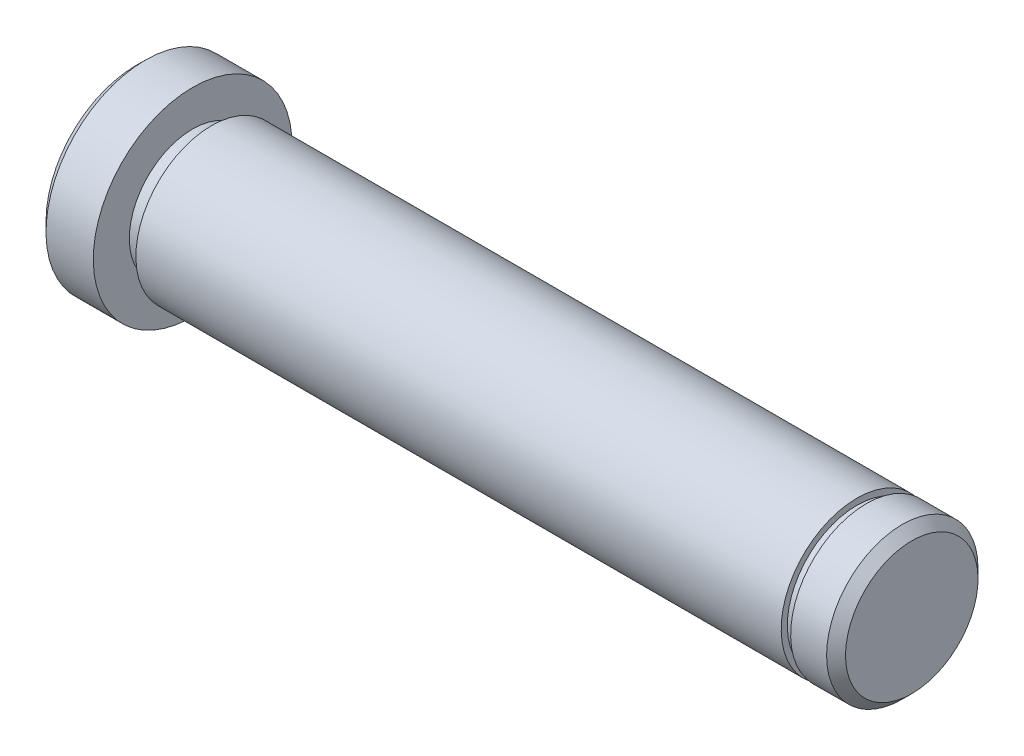
SolidWorks part; units mm, degrees
ref_plane "前视基准面" through (0, 0, 0) normal (0, 0, 1) x (1, 0, 0)
ref_plane "上视基准面" through (0, 0, 0) normal (0, 1, 0) x (1, 0, 0)
ref_plane "右视基准面" through (0, 0, 0) normal (1, 0, 0) x (0, 0, -1)
other "Configuration Table"
sketch "草图1" plane through (0, 0, 0) normal (0, 0, 1) x (1, 0, 0)
  line L0 (0, 0) -> (36.475, 0) construction
  line L1 (0, 0) -> (0, 10.5)
  line L2 (0, 10.5) -> (6, 10.5)
  line L3 (6, 10.5) -> (6, 8)
  line L4 (6, 8) -> (82, 8)
  line L5 (82, 8) -> (82, 0)
  line L6 (82, 0) -> (0, 0)
  line L7 (6, 8) -> (6, 6.6919)
  line L8 (6, 6.6919) -> (8, 6.6919)
  line L9 (8, 6.6919) -> (8, 8)
  line L10 (76.2, 8) -> (76.2, 7.35)
  line L11 (76.2, 7.35) -> (77.2, 7.35)
  line L12 (77.2, 7.35) -> (77.2, 8)
  dimension "D1" = 10.5
  dimension "D2" = 6
  dimension "D3" = 8
  dimension "D4" = 82
  dimension "D5" = 2
  dimension "D6" = 1.3081
  dimension "D7" = 7.35
  dimension "D8" = 1
  dimension "D9" = 70.2
revolve "旋转1" add sketch "草图1" angle 360 about L6
chamfer "倒角1" distance 1 angle 45 2 edges at (82, 8, 0) (0, 10.5, 0)
